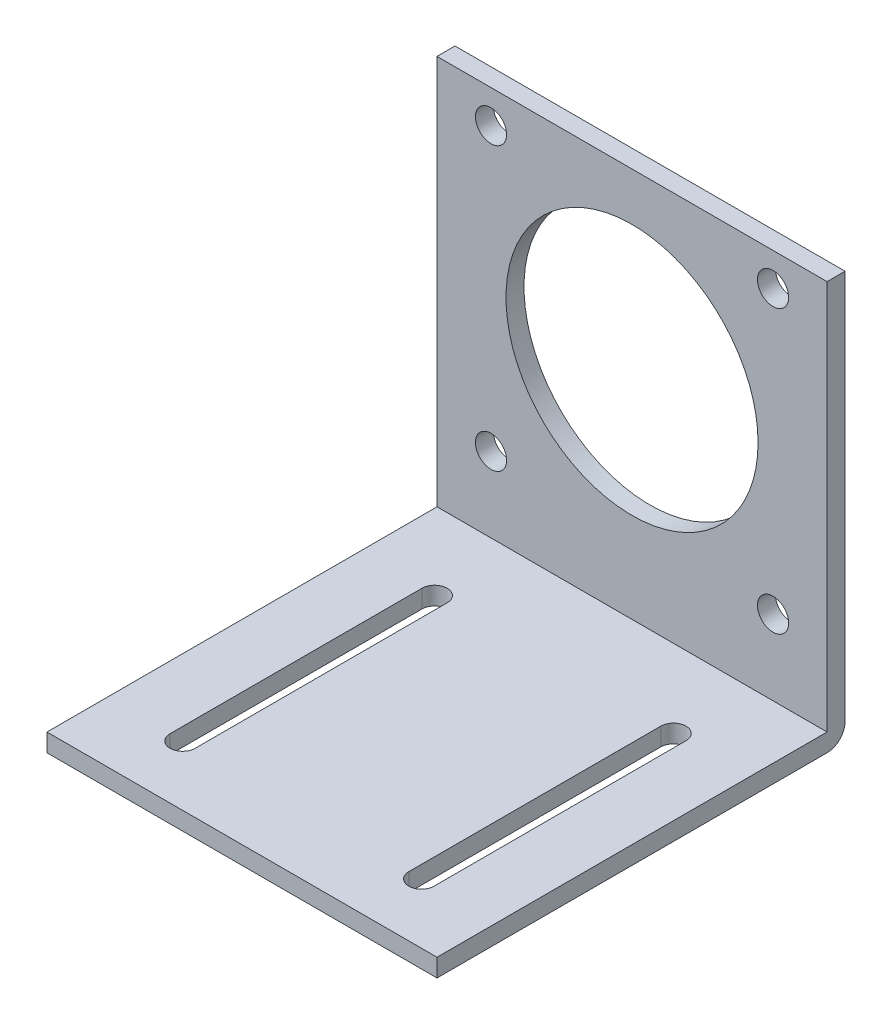
SolidWorks part; units mm, degrees
ref_plane "前视基准面" through (0, 0, 0) normal (0, 0, 1) x (1, 0, 0)
ref_plane "上视基准面" through (0, 0, 0) normal (0, 1, 0) x (1, 0, 0)
ref_plane "右视基准面" through (0, 0, 0) normal (1, 0, 0) x (0, 0, -1)
sketch "草图1" plane through (0, 0, 0) normal (0, 0, 1) x (1, 0, 0)
  line L1 (-32.5, 34) -> (32.5, 34)
  line L2 (-32.5, 34) -> (-32.5, -34)
  line L3 (-32.5, -34) -> (32.5, -34)
  line L4 (32.5, 34) -> (32.5, -34)
  line L5 (-32.5, 34) -> (32.5, -34) construction
  line L6 (-32.5, -34) -> (32.5, 34) construction
  line L7 (-23.5, 28.5) -> (23.5, 28.5) construction
  line L8 (-23.5, 28.5) -> (-23.5, -18.5) construction
  line L9 (-23.5, -18.5) -> (23.5, -18.5) construction
  line L10 (23.5, 28.5) -> (23.5, -18.5) construction
  line L11 (-23.5, 28.5) -> (23.5, -18.5) construction
  line L12 (-23.5, -18.5) -> (23.5, 28.5) construction
  circle A0 centre (0, 5) radius 21
  circle A1 centre (23.5, 28.5) radius 2.6
  circle A2 centre (-23.5, 28.5) radius 2.6
  circle A3 centre (-23.5, -18.5) radius 2.6
  circle A4 centre (23.5, -18.5) radius 2.6
  point P0 (0, 0)
  dimension "D4" = 42
  dimension "D7" = 5.2
  dimension "D8" = 5.2
  dimension "D9" = 5.2
  dimension "D10" = 5.2
  dimension "D1" = 68
  dimension "D2" = 65
  dimension "D3" = 29
  dimension "D5" = 47
  dimension "D6" = 47
extrude "凸台-拉伸1" add sketch "草图1" along normal blind 3
ref_plane "基准面1" through (0, 0, 3) normal (0, 0, 1) x (1, 0, 0)
sketch "草图2" plane through (0, 0, 3) normal (0, 0, 1) x (1, 0, 0)
  line L0 (32.5, -34) -> (32.5, 34) construction
  line L1 (-32.5, -34) -> (32.5, -34)
  line L2 (-32.5, -34) -> (-32.5, -31)
  line L3 (-32.5, -31) -> (32.5, -31)
  line L4 (32.5, -34) -> (32.5, -31)
  dimension "D1" = 3
extrude "凸台-拉伸2" add sketch "草图2" along normal blind 65
ref_plane "基准面2" through (0, -31, 0) normal (0, 1, 0) x (1, 0, 0)
sketch "草图3" plane through (0, -31, 0) normal (0, 1, 0) x (1, 0, 0)
  line L0 (0, 0) -> (0, -68) construction
  line L1 (32.5, 0) -> (-32.5, 0) construction
  line L2 (32.5, -68) -> (-32.5, -68) construction
  line L3 (19.9, -16) -> (19.9, -58) construction
  line L4 (22, -16) -> (22, -58)
  line L5 (17.8, -16) -> (17.8, -58)
  line L6 (32.5, -68) -> (32.5, -3) construction
  line L9 (-19.9, -16) -> (-19.9, -58) construction
  line L10 (-22, -16) -> (-22, -58)
  line L11 (-17.8, -16) -> (-17.8, -58)
  arc A0 (22, -16) -> (17.8, -16) centre (19.9, -16) ccw
  arc A1 (17.8, -58) -> (22, -58) centre (19.9, -58) ccw
  arc A2 (-22, -16) -> (-17.8, -16) centre (-19.9, -16) cw
  arc A3 (-17.8, -58) -> (-22, -58) centre (-19.9, -58) cw
  point P8 (19.9, -37)
  point P19 (-19.9, -37)
  dimension "D2" = 10
  dimension "D3" = 42
  dimension "D4" = 2.1
  dimension "D1" = 10.5
extrude "切除-拉伸1" cut sketch "草图3" against normal blind 65
fillet "圆角1" radius 3 1 edges at (0, -34, 0)
